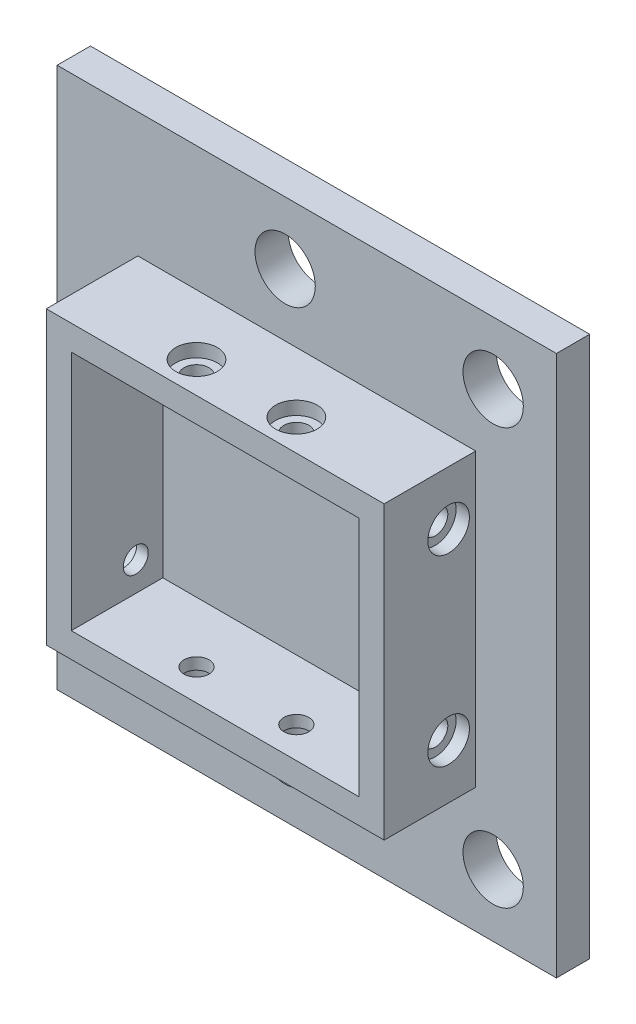
SolidWorks part; units mm, degrees
ref_plane "정면" through (0, 0, 0) normal (0, 0, 1) x (1, 0, 0)
ref_plane "윗면" through (0, 0, 0) normal (0, 1, 0) x (1, 0, 0)
ref_plane "우측면" through (0, 0, 0) normal (1, 0, 0) x (0, 0, -1)
sketch "스케치1" plane through (0, 0, 0) normal (0, 0, 1) x (1, 0, 0)
  line L0 (0, 32.5) -> (0, -32.5) construction
  line L1 (30, -32.5) -> (-30, -32.5)
  line L2 (30, -32.5) -> (30, 32.5)
  line L3 (30, 32.5) -> (-30, 32.5)
  line L4 (-30, -32.5) -> (-30, 32.5)
  line L5 (30, -32.5) -> (-30, 32.5) construction
  line L6 (30, 32.5) -> (-30, -32.5) construction
  line L7 (-2.6, 32.5) -> (-2.6, -32.5) construction
  line L8 (22.4, 32.5) -> (22.4, -32.5) construction
  line L10 (17, -14.25) -> (-17, -14.25) construction
  line L11 (17, -14.25) -> (17, 14.25) construction
  line L12 (17, 14.25) -> (-17, 14.25) construction
  line L13 (-17, -14.25) -> (-17, 14.25) construction
  line L14 (17, -14.25) -> (-17, 14.25) construction
  line L15 (17, 14.25) -> (-17, -14.25) construction
  circle A0 centre (-2.6, 25) radius 3.625
  circle A1 centre (-2.6, -25) radius 3.625
  circle A2 centre (22.4, 25) radius 3.625
  circle A3 centre (22.4, -25) radius 3.625
  point P0 (0, 0)
  point P12 (0, 0)
  point P27 (-2.6, 0)
  dimension "D7" = 7.25
  dimension "D1" = 2.6
  dimension "D2" = 25
  dimension "D3" = 28.5
  dimension "D4" = 34
  dimension "D5" = 65
  dimension "D6" = 60
  dimension "D8" = 25
  dimension "D9" = 25
extrude "보스-돌출1" add sketch "스케치1" along normal blind 4
sketch "스케치2" plane through (0, 0, 4) normal (0, 0, 1) x (1, 0, 0)
  line L1 (17.3, -14.5) -> (-17.3, -14.5)
  line L2 (17.3, -14.5) -> (17.3, 14.5)
  line L3 (17.3, 14.5) -> (-17.3, 14.5)
  line L4 (-17.3, -14.5) -> (-17.3, 14.5)
  line L5 (17.3, -14.5) -> (-17.3, 14.5) construction
  line L6 (17.3, 14.5) -> (-17.3, -14.5) construction
  line L7 (20.3, -17.5) -> (-20.3, -17.5)
  line L8 (20.3, -17.5) -> (20.3, 17.5)
  line L9 (20.3, 17.5) -> (-20.3, 17.5)
  line L10 (-20.3, -17.5) -> (-20.3, 17.5)
  line L11 (20.3, -17.5) -> (-20.3, 17.5) construction
  line L12 (20.3, 17.5) -> (-20.3, -17.5) construction
  point P0 (0, 0)
  point P6 (0, 0)
  dimension "D1" = 34.6
  dimension "D2" = 29
  dimension "D3" = 35
  dimension "D4" = 40.6
extrude "보스-돌출2" add sketch "스케치2" along normal blind 11
sketch "스케치3" plane through (0, -17.5, 0) normal (0, -1, 0) x (1, 0, 0)
  line L0 (0, 0) -> (0, 15) construction
  line L1 (-30, 0) -> (30, 0) construction
  line L2 (-20.3, 15) -> (20.3, 15) construction
  line L3 (-30, 4) -> (30, 4) construction
  circle A0 centre (-6, 11.25) radius 1.5
  circle A1 centre (6, 11.25) radius 1.5
  dimension "D1" = 3
  dimension "D2" = 7.25
  dimension "D3" = 12
extrude "컷-돌출1" cut sketch "스케치3" against normal through all
sketch "스케치4" plane through (0, -17.5, 0) normal (0, -1, 0) x (1, 0, 0)
  line L0 (0, 0) -> (0, 15) construction
  line L1 (-20.3, 15) -> (20.3, 15) construction
  circle A0 centre (-6, 11.25) radius 2.5
  circle A1 centre (6, 11.25) radius 2.5
  dimension "D1" = 5
extrude "컷-돌출2" cut sketch "스케치4" against normal blind 1.6
mirror "대칭 복사1" about plane through (0, 0, 0) normal (0, 1, 0) of "컷-돌출2"
sketch "스케치5" plane through (-20.3, 0, 0) normal (-1, 0, 0) x (0, 0, 1)
  line L0 (0, 0) -> (15, 0) construction
  line L1 (0, 32.5) -> (0, -32.5) construction
  line L2 (15, 17.5) -> (15, -17.5) construction
  line L3 (4, 32.5) -> (4, -32.5) construction
  circle A0 centre (7.25, -11) radius 1.5
  circle A1 centre (7.25, 11) radius 1.5
  dimension "D1" = 3
  dimension "D2" = 11
  dimension "D3" = 3.25
extrude "컷-돌출3" cut sketch "스케치5" against normal through all
sketch "스케치6" plane through (-20.3, 0, 0) normal (-1, 0, 0) x (0, 0, 1)
  line L0 (0, 0) -> (15, 0) construction
  line L1 (15, 17.5) -> (15, -17.5) construction
  circle A0 centre (7.25, 11) radius 2.5
  circle A1 centre (7.25, -11) radius 2.5
  dimension "D1" = 5
extrude "컷-돌출4" cut sketch "스케치6" against normal blind 1.6
mirror "대칭 복사2" about plane through (0, 0, 0) normal (1, 0, 0) of "컷-돌출4"
